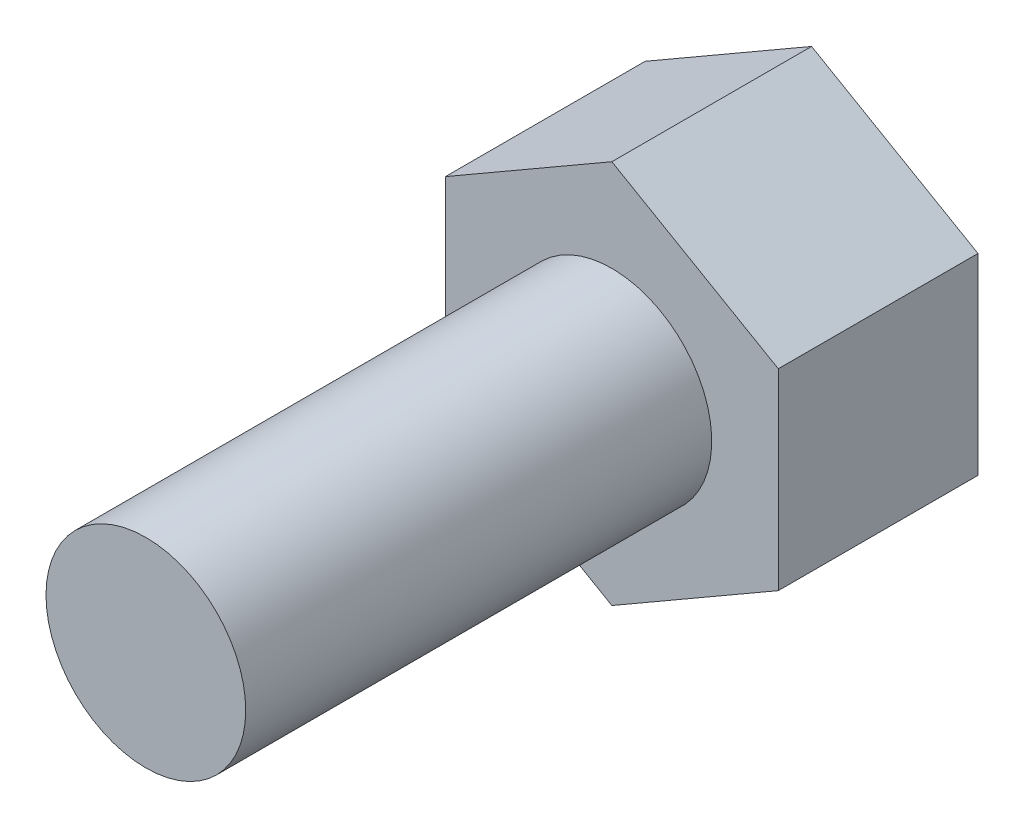
SolidWorks part; units mm, degrees
ref_plane "Front Plane" through (0, 0, 0) normal (0, 0, 1) x (1, 0, 0)
ref_plane "Top Plane" through (0, 0, 0) normal (0, 1, 0) x (1, 0, 0)
ref_plane "Right Plane" through (0, 0, 0) normal (1, 0, 0) x (0, 0, -1)
sketch "Sketch1" plane through (0, 0, 0) normal (0, 0, 1) x (1, 0, 0)
  circle A0 centre (-63.4948, 14.9787) radius 1.5
extrude "Boss-Extrude1" add sketch "Sketch1" along normal blind 7
sketch "Sketch2" plane through (0, 0, 0) normal (0, 0, -1) x (-1, 0, 0)
  line L1 (63.4948, 12.092) -> (65.9948, 13.5353)
  line L2 (65.9948, 13.5353) -> (65.9948, 16.4221)
  line L3 (65.9948, 16.4221) -> (63.4948, 17.8655)
  line L4 (63.4948, 17.8655) -> (60.9948, 16.4221)
  line L5 (60.9948, 16.4221) -> (60.9948, 13.5353)
  line L6 (60.9948, 13.5353) -> (63.4948, 12.092)
  circle A0 centre (63.4948, 14.9787) radius 2.5 construction
  dimension "D1" = 5
extrude "Boss-Extrude2" add sketch "Sketch2" along normal blind 3
